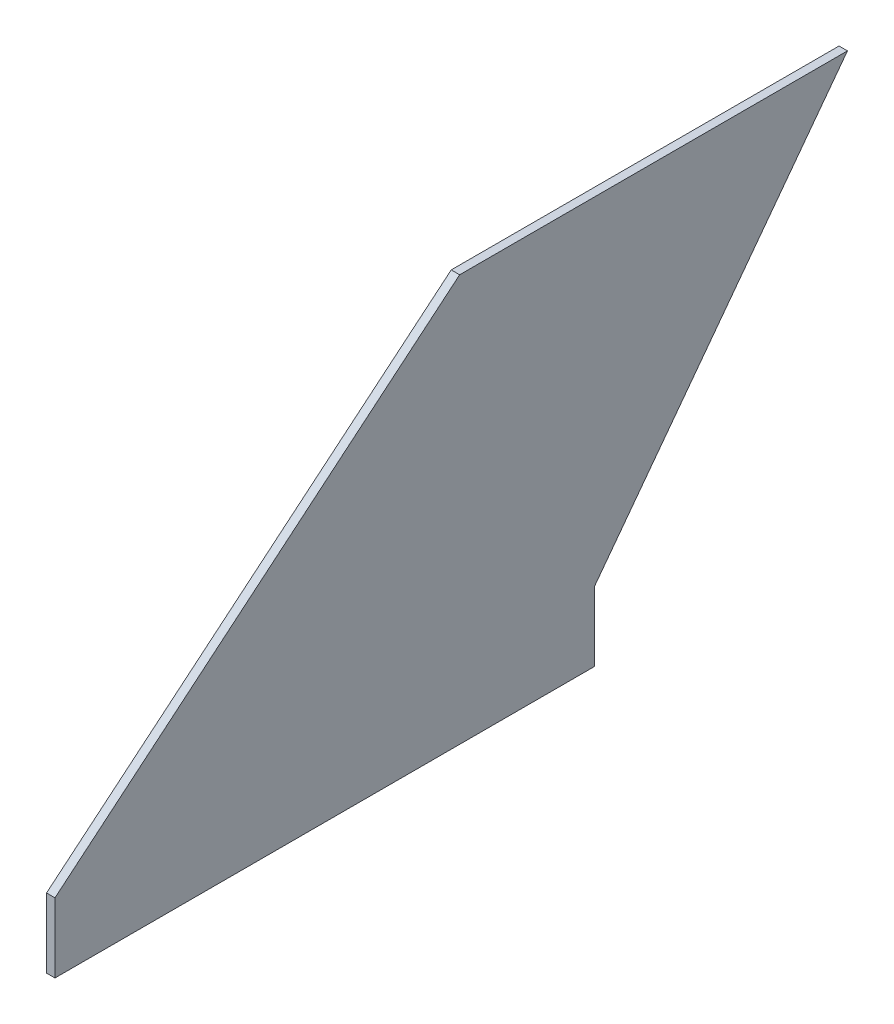
SolidWorks part; units mm, degrees
ref_plane "Front Plane" through (0, 0, 0) normal (0, 0, 1) x (1, 0, 0)
ref_plane "Top Plane" through (0, 0, 0) normal (0, 1, 0) x (1, 0, 0)
ref_plane "Right Plane" through (0, 0, 0) normal (1, 0, 0) x (0, 0, -1)
sketch "Sketch2" plane through (0, 0, 0) normal (1, 0, 0) x (0, 0, -1)
  line L0 (0, 0) -> (152.4, 127)
  line L1 (0, -26.1493) -> (203.2, -26.1493)
  line L2 (0, -26.1493) -> (0, 0)
  line L3 (0, 0) -> (203.2, 0) construction
  line L4 (203.2, -26.1493) -> (203.2, 0)
  line L5 (0, -26.1493) -> (203.2, 0) construction
  line L6 (0, 0) -> (203.2, -26.1493) construction
  line L7 (152.4, 127) -> (298.45, 127)
  line L8 (298.45, 127) -> (203.2, 0)
  point P0 (101.6, -13.0746)
  dimension "D1" = 152.4
  dimension "D2" = 127
  dimension "D3" = 298.45
  dimension "D4" = 203.2
  dimension "D5" = 26.1493
extrude "Boss-Extrude1" add sketch "Sketch2" along normal blind 3.175
equation "\"AIRFRAME_OD\"= 5.15in"
equation "\"AIRFRAME_ID\"= 4.99in"
equation "\"FLAT_T\"= 0.125in"
equation "\"COUPLER_OD\"= 4.998in"
equation "\"COUPLER_ID\"= 4.85in"
equation "\"NOSE_EXP_L\"= 27in"
equation "\"NOSE_SHOULDER_L\"= 5in"
equation "\"MAIN_L\"= 30in"
equation "\"RECO_COUP_L\"= 10in"
equation "\"RECO_SWITCH_L\"= 2in"
equation "\"RECO_ROD_X\"= 3.5in"
equation "\"DROGUE_L\"= 20in"
equation "\"ATS_FORE_COUP_L\"= 5.5in"
equation "\"ATS_AFT_COUP_L\"= 4.5in"
equation "\"ATS_ROD_X\"= 3.75in"
equation "\"LOWER_L\"= 30in"
equation "\"FIN_ROOT\"= 8in"
equation "\"FIN_X\"= 0.75in"
equation "\"FIN_N\"= 4"
equation "\"MOTOR_OD\"= 3.091in"
equation "\"MOTOR_ID\"= 3.00in"
equation "\"MOTOR_L\"= 14in"
equation "\"CR_AFT_X\"= 0.5in"
equation "\"CR_FORE_X\"= 9.25in"
equation "\"D1@Boss-Extrude1\"=\"FLAT_T\""
equation "\"D4@Sketch2\"=\"FIN_ROOT\""
equation "\"D5@Sketch2\"=(\"AIRFRAME_OD\"-\"MOTOR_OD\")*0.5"
equation "\"MOTOR_LOWER_X\"= 2in"
